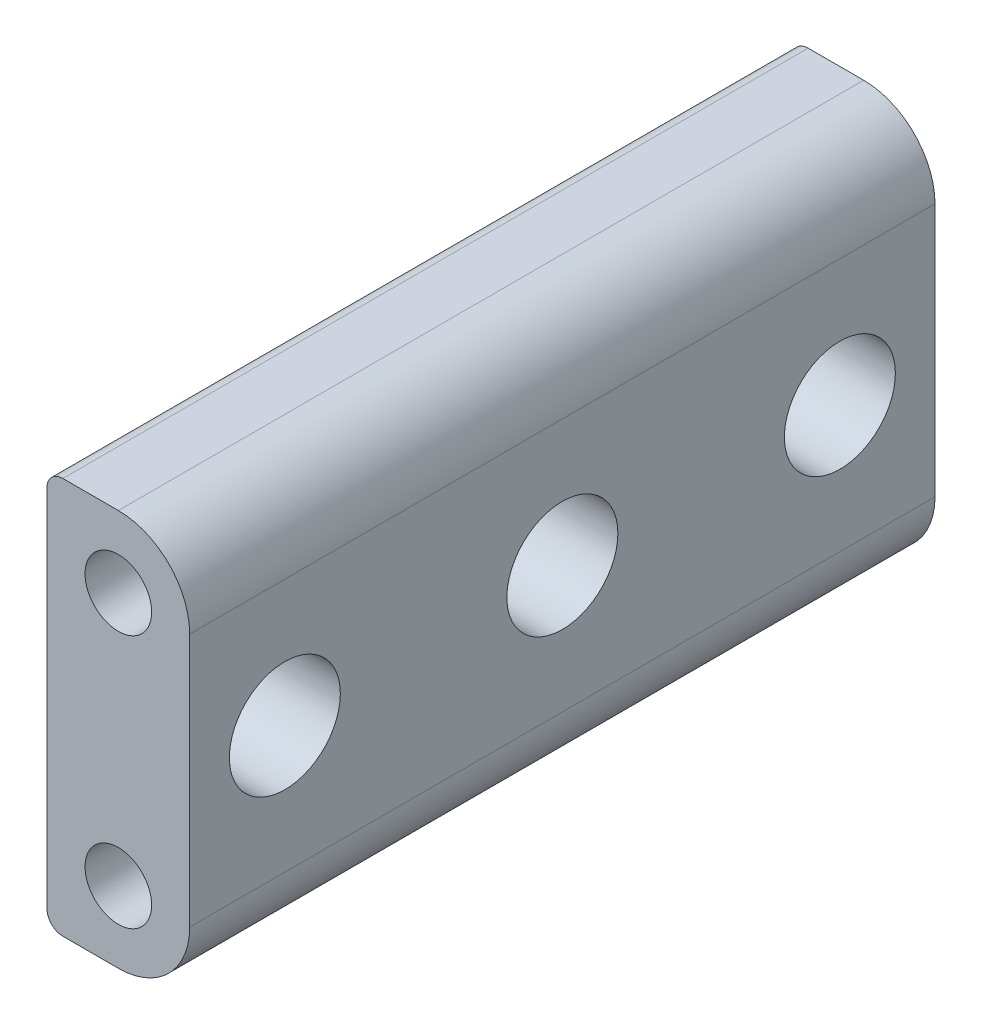
SolidWorks part; units mm, degrees
ref_plane "Front Plane" through (0, 0, 0) normal (0, 0, 1) x (1, 0, 0)
ref_plane "Top Plane" through (0, 0, 0) normal (0, 1, 0) x (1, 0, 0)
ref_plane "Right Plane" through (0, 0, 0) normal (1, 0, 0) x (0, 0, -1)
sketch "Sketch1" plane through (0, 0, 0) normal (0, 0, 1) x (1, 0, 0)
  line L0 (0, 0) -> (0, 16) construction
  line L1 (-4.5, -4.5) -> (-4.5, 20.5)
  line L2 (4.5, 0) -> (4.5, 16)
  line L5 (0, 20.5) -> (-4.5, 20.5)
  line L6 (0, -4.5) -> (-4.5, -4.5)
  arc A0 (0, -4.5) -> (4.5, 0) centre (0, 0) ccw
  arc A2 (0, 20.5) -> (4.5, 16) centre (0, 16) cw
  point P3 (0, 8)
  dimension "D1" = 4.5
  dimension "D2" = 16
extrude "Boss-Extrude1" add sketch "Sketch1" along normal blind 47
sketch "Sketch2" plane through (0, 0, 47) normal (0, 0, 1) x (1, 0, 0)
  circle A0 centre (0, 16) radius 2.1
  circle A1 centre (0, 0) radius 2.1
  dimension "D1" = 4.2
extrude "Cut-Extrude1" cut sketch "Sketch2" against normal blind 4
sketch "Sketch3" plane through (0, 0, 0) normal (0, 0, -1) x (-1, 0, 0)
  circle A1 centre (0, 0) radius 2.1
  circle A2 centre (0, 0) radius 2.1
  circle A3 centre (0, 16) radius 2.1
  circle A4 centre (0, 16) radius 2.1
  dimension "D1" = 0
  dimension "D2" = 0
extrude "Cut-Extrude2" cut sketch "Sketch3" against normal blind 4
sketch "Sketch4" plane through (4.5, 0, 0) normal (1, 0, 0) x (0, 0, -1)
  line L0 (-47, 8) -> (0, 8) construction
  line L1 (-47, 0) -> (-47, 16) construction
  line L2 (0, 0) -> (0, 16) construction
  line L3 (0, 8) -> (-23.5, 20.5) construction
  line L5 (-23.5, 20.5) -> (-23.5, 8) construction
  line L6 (-47, 20.5) -> (0, 20.5) construction
  circle A0 centre (-41, 8) radius 3.5
  circle A1 centre (-23.5, 8) radius 3.5
  circle A2 centre (-6, 8) radius 3.5
  dimension "D2" = 7
  dimension "D1" = 35
extrude "Cut-Extrude3" cut sketch "Sketch4" against normal blind 5
fillet "Fillet1" radius 1 2 edges at (-4.5, -4.5, 23.5) (-4.5, 20.5, 23.5)
